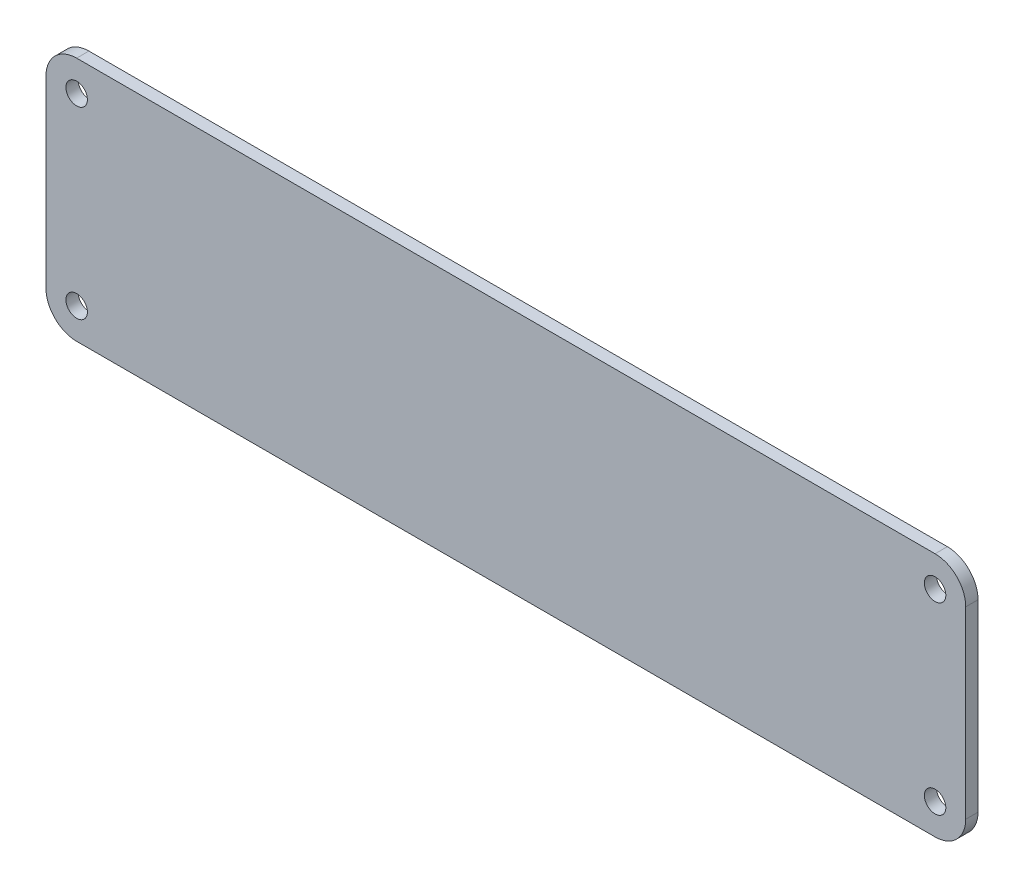
SolidWorks part; units mm, degrees
ref_plane "Front Plane" through (0, 0, 0) normal (0, 0, 1) x (1, 0, 0)
ref_plane "Top Plane" through (0, 0, 0) normal (0, 1, 0) x (1, 0, 0)
ref_plane "Right Plane" through (0, 0, 0) normal (1, 0, 0) x (0, 0, -1)
sketch "Sketch1" plane through (0, 0, 0) normal (0, 0, 1) x (1, 0, 0)
  line L1 (75, -20) -> (-75, -20)
  line L2 (75, -20) -> (75, 20)
  line L3 (75, 20) -> (-75, 20)
  line L4 (-75, -20) -> (-75, 20)
  line L5 (75, -20) -> (-75, 20) construction
  line L6 (75, 20) -> (-75, -20) construction
  point P0 (0, 0)
  dimension "D1" = 40
  dimension "D2" = 150
extrude "Boss-Extrude1" add sketch "Sketch1" along normal blind 2
sketch "Sketch2" plane through (0, 0, 2) normal (0, 0, 1) x (1, 0, 0)
  line L0 (75, 20) -> (-75, 20) construction
  line L1 (70, -15) -> (-70, -15) construction
  line L2 (70, -15) -> (70, 15) construction
  line L3 (70, 15) -> (-70, 15) construction
  line L4 (-70, -15) -> (-70, 15) construction
  line L5 (70, -15) -> (-70, 15) construction
  line L6 (70, 15) -> (-70, -15) construction
  line L7 (-75, 20) -> (-75, -20) construction
  circle A0 centre (-70, 15) radius 1.75
  circle A1 centre (-70, -15) radius 1.75
  circle A2 centre (70, -15) radius 1.75
  circle A3 centre (70, 15) radius 1.75
  point P0 (0, 0)
  dimension "D1" = 3.5
  dimension "D2" = 5
  dimension "D3" = 5
extrude "Cut-Extrude1" cut sketch "Sketch2" against normal through all
fillet "Fillet1" radius 5 4 edges at (75, -20, 1) (75, 20, 1) (-75, -20, 1) (-75, 20, 1)
